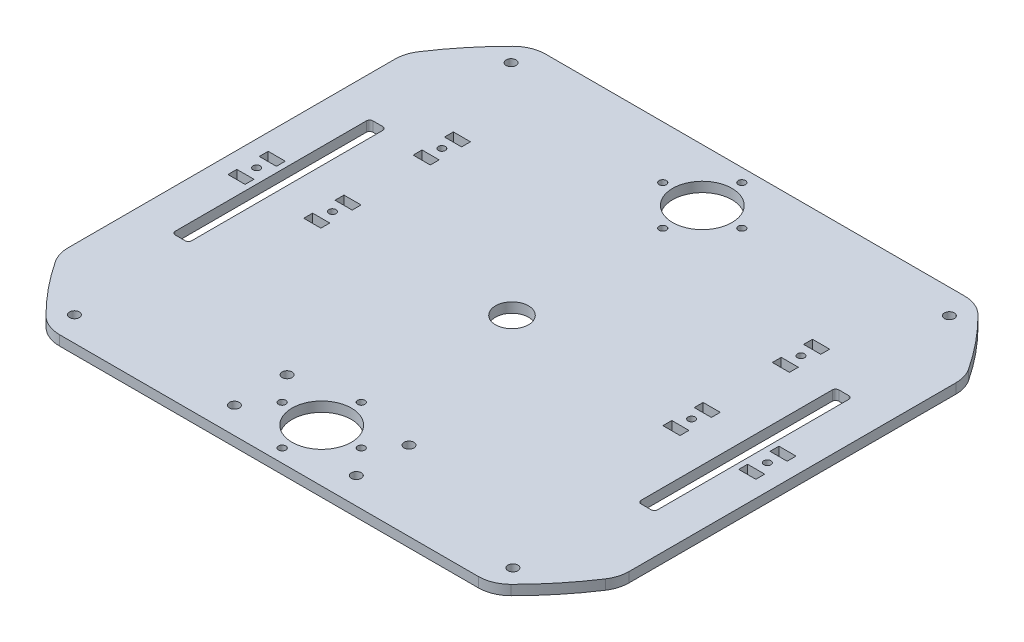
SolidWorks part; units mm, degrees
ref_plane "Front Plane" through (0, 0, 0) normal (0, 0, 1) x (1, 0, 0)
ref_plane "Top Plane" through (0, 0, 0) normal (0, 1, 0) x (1, 0, 0)
ref_plane "Right Plane" through (0, 0, 0) normal (1, 0, 0) x (0, 0, -1)
sketch "Sketch1" plane through (0, 0, 0) normal (0, 1, 0) x (1, 0, 0)
  circle A0 centre (0, 0) radius 100
  circle A1 centre (0, 0) radius 5
  dimension "D1" = 200
  dimension "D2" = 10
extrude "Boss-Extrude1" add sketch "Sketch1" along normal blind 3
sketch "Sketch2" plane through (0, 3, 0) normal (0, 1, 0) x (1, 0, 0)
  line L0 (75, 6) -> (80, 6) construction
  line L1 (75, 6) -> (75, 3.5) construction
  line L2 (75, 3.5) -> (80, 3.5) construction
  line L3 (80, 6) -> (80, 3.5) construction
  line L4 (75, -3.5) -> (80, -3.5) construction
  line L5 (75, -3.5) -> (75, -6) construction
  line L6 (75, -6) -> (80, -6) construction
  line L7 (80, -3.5) -> (80, -6) construction
  line L8 (66, -59.6098) -> (66, 6) construction
  line L9 (52, -3.5) -> (52, -6) construction
  line L10 (57, -6) -> (52, -6) construction
  line L11 (57, -3.5) -> (57, -6) construction
  line L12 (57, -3.5) -> (52, -3.5) construction
  line L13 (52, 6) -> (52, 3.5) construction
  line L14 (57, 3.5) -> (52, 3.5) construction
  line L15 (57, 6) -> (57, 3.5) construction
  line L16 (57, 6) -> (52, 6) construction
  line L17 (55.9387, 16.6) -> (52, 16.6) construction
  line L18 (57, 27.2) -> (52, 27.2) construction
  line L19 (57, 27.2) -> (57, 29.7) construction
  line L20 (57, 29.7) -> (52, 29.7) construction
  line L21 (52, 27.2) -> (52, 29.7) construction
  line L22 (57, 36.7) -> (52, 36.7) construction
  line L23 (57, 36.7) -> (57, 39.2) construction
  line L24 (57, 39.2) -> (52, 39.2) construction
  line L25 (52, 36.7) -> (52, 39.2) construction
  line L26 (0, 85.9128) -> (0, -59.0872) construction
  line L27 (-55.9387, 16.6) -> (-52, 16.6) construction
  line L28 (-66, -59.6098) -> (-66, 6) construction
  line L29 (-52, 36.7) -> (-52, 39.2) construction
  line L30 (-57, 39.2) -> (-52, 39.2) construction
  line L31 (-57, 36.7) -> (-57, 39.2) construction
  line L32 (-57, 36.7) -> (-52, 36.7) construction
  line L33 (-52, 27.2) -> (-52, 29.7) construction
  line L34 (-57, 29.7) -> (-52, 29.7) construction
  line L35 (-57, 27.2) -> (-57, 29.7) construction
  line L36 (-57, 27.2) -> (-52, 27.2) construction
  line L37 (-57, 6) -> (-52, 6) construction
  line L38 (-57, 6) -> (-57, 3.5) construction
  line L39 (-57, 3.5) -> (-52, 3.5) construction
  line L40 (-52, 6) -> (-52, 3.5) construction
  line L41 (-57, -3.5) -> (-52, -3.5) construction
  line L42 (-57, -3.5) -> (-57, -6) construction
  line L43 (-57, -6) -> (-52, -6) construction
  line L44 (-52, -3.5) -> (-52, -6) construction
  line L45 (-80, -3.5) -> (-80, -6) construction
  line L46 (-75, -6) -> (-80, -6) construction
  line L47 (-75, -3.5) -> (-75, -6) construction
  line L48 (-75, -3.5) -> (-80, -3.5) construction
  line L49 (-80, 6) -> (-80, 3.5) construction
  line L50 (-75, 3.5) -> (-80, 3.5) construction
  line L51 (-75, 6) -> (-75, 3.5) construction
  line L52 (-75, 6) -> (-80, 6) construction
  line L101 (-51.9, 36.6) -> (-51.9, 39.3)
  line L102 (-57.1, 39.3) -> (-51.9, 39.3)
  line L103 (-57.1, 36.6) -> (-57.1, 39.3)
  line L104 (-57.1, 36.6) -> (-51.9, 36.6)
  line L105 (-51.9, 27.1) -> (-51.9, 29.8)
  line L106 (-57.1, 29.8) -> (-51.9, 29.8)
  line L107 (-57.1, 27.1) -> (-57.1, 29.8)
  line L108 (-57.1, 27.1) -> (-51.9, 27.1)
  line L109 (-57.1, 6.1) -> (-51.9, 6.1)
  line L110 (-51.9, 6.1) -> (-51.9, 3.4)
  line L111 (-57.1, 3.4) -> (-51.9, 3.4)
  line L112 (-57.1, 6.1) -> (-57.1, 3.4)
  line L113 (-57.1, -3.4) -> (-51.9, -3.4)
  line L114 (-51.9, -3.4) -> (-51.9, -6.1)
  line L115 (-57.1, -6.1) -> (-51.9, -6.1)
  line L116 (-57.1, -3.4) -> (-57.1, -6.1)
  line L117 (-80.1, -3.4) -> (-80.1, -6.1)
  line L118 (-74.9, -6.1) -> (-80.1, -6.1)
  line L119 (-74.9, -3.4) -> (-74.9, -6.1)
  line L120 (-74.9, -3.4) -> (-80.1, -3.4)
  line L121 (-80.1, 6.1) -> (-80.1, 3.4)
  line L122 (-74.9, 3.4) -> (-80.1, 3.4)
  line L123 (-74.9, 6.1) -> (-74.9, 3.4)
  line L124 (-74.9, 6.1) -> (-80.1, 6.1)
  line L125 (57.1, 27.1) -> (51.9, 27.1)
  line L126 (51.9, 27.1) -> (51.9, 29.8)
  line L127 (57.1, 29.8) -> (51.9, 29.8)
  line L128 (57.1, 27.1) -> (57.1, 29.8)
  line L129 (57.1, 36.6) -> (51.9, 36.6)
  line L130 (51.9, 36.6) -> (51.9, 39.3)
  line L131 (57.1, 39.3) -> (51.9, 39.3)
  line L132 (57.1, 36.6) -> (57.1, 39.3)
  line L133 (74.9, 6.1) -> (80.1, 6.1)
  line L134 (80.1, 6.1) -> (80.1, 3.4)
  line L135 (74.9, 3.4) -> (80.1, 3.4)
  line L136 (74.9, 6.1) -> (74.9, 3.4)
  line L137 (74.9, -3.4) -> (80.1, -3.4)
  line L138 (80.1, -3.4) -> (80.1, -6.1)
  line L139 (74.9, -6.1) -> (80.1, -6.1)
  line L140 (74.9, -3.4) -> (74.9, -6.1)
  line L141 (51.9, -3.4) -> (51.9, -6.1)
  line L142 (57.1, -6.1) -> (51.9, -6.1)
  line L143 (57.1, -3.4) -> (57.1, -6.1)
  line L144 (57.1, -3.4) -> (51.9, -3.4)
  line L145 (51.9, 6.1) -> (51.9, 3.4)
  line L146 (57.1, 3.4) -> (51.9, 3.4)
  line L147 (57.1, 6.1) -> (57.1, 3.4)
  line L148 (57.1, 6.1) -> (51.9, 6.1)
  line L149 (-51.9, 3.4) -> (-51.9, -3.4) construction
  point P21 (54.5, 6)
  point P59 (-51.9, 0)
  dimension "D1" = 2.5
  dimension "D2" = 5
  dimension "D3" = 7
  dimension "D4" = 9
  dimension "D5" = 10.6
  dimension "D6" = 52
  dimension "D7" = 0.1
extrude "Cut-Extrude1" cut sketch "Sketch2" against normal through all
sketch "Sketch3" plane through (0, 3, 0) normal (0, 1, 0) x (1, 0, 0)
  line L0 (-85.1, 52.5166) -> (-85.1, -52.5166)
  line L1 (-80.1, 6.1) -> (-80.1, 3.4) construction
  line L2 (85.1, 52.5166) -> (85.1, -52.5166)
  line L3 (80.1, -6.1) -> (80.1, -3.4) construction
  line L4 (-67.5347, 73.75) -> (67.5347, 73.75)
  line L5 (-67.5347, -73.75) -> (67.5347, -73.75)
  line L7 (-67.5347, 73.75) -> (-67.5347, 115.6707)
  line L8 (-67.5347, 115.6707) -> (67.5347, 115.6707)
  line L9 (67.5347, 115.6707) -> (67.5347, 73.75)
  line L10 (85.1, 52.5166) -> (140.5183, 52.5166)
  line L11 (140.5183, 52.5166) -> (140.5183, -52.5166)
  line L12 (140.5183, -52.5166) -> (85.1, -52.5166)
  line L13 (67.5347, -73.75) -> (67.5347, -121.8499)
  line L14 (67.5347, -121.8499) -> (-67.5347, -121.8499)
  line L15 (-67.5347, -121.8499) -> (-67.5347, -73.75)
  line L16 (-85.1, -52.5166) -> (-115.9325, -52.5166)
  line L17 (-115.9325, -52.5166) -> (-115.9325, 52.5166)
  line L18 (-115.9325, 52.5166) -> (-85.1, 52.5166)
  circle A0 centre (0, 0) radius 100 construction
  point P7 (-80.1, 4.75)
  circle M53 centre (0, 0) radius 100
  dimension "D1" = 5
  dimension "D2" = 5
  dimension "D3" = 147.5
extrude "Cut-Extrude2" cut sketch "Sketch3" against normal through all contours L4 M53 | L0 M53 | L5 M53 | L2 M53
sketch "Sketch4" plane through (0, 3, 0) normal (0, 1, 0) x (1, 0, 0)
  line L0 (-74.9, 3.4) -> (-74.9, 6.1) construction
  line L1 (-73.2, 30) -> (-68.2, 30)
  line L2 (-73.2, 30) -> (-73.2, -30)
  line L3 (-73.2, -30) -> (-68.2, -30)
  line L4 (-68.2, 30) -> (-68.2, -30)
  line L5 (-74.9, 3.4) -> (-74.9, -3.4) construction
  line L6 (0, 0) -> (0, 73.75) construction
  line L7 (-67.5347, 73.75) -> (67.5347, 73.75) construction
  line L8 (73.2, 30) -> (68.2, 30)
  line L9 (73.2, 30) -> (73.2, -30)
  line L10 (73.2, -30) -> (68.2, -30)
  line L11 (68.2, 30) -> (68.2, -30)
  point P10 (-73.2, 0)
  point P11 (-74.9, 0)
  dimension "D1" = 1.7
  dimension "D2" = 5
  dimension "D3" = 60
extrude "Cut-Extrude3" cut sketch "Sketch4" against normal through all
fillet "Fillet3" radius 10 8 edges at (-85.1, 1.5, -52.5166) (-85.1, 1.5, 52.5166) (-67.5347, 1.5, 73.75) (67.5347, 1.5, 73.75) (85.1, 1.5, 52.5166) (85.1, 1.5, -52.5166) (67.5347, 1.5, -73.75) (-67.5347, 1.5, -73.75)
fillet "Fillet2" radius 1 8 edges at (68.2, 1.5, -30) (73.2, 1.5, -30) (68.2, 1.5, 30) (73.2, 1.5, 30) (-68.2, 1.5, 30) (-73.2, 1.5, 30) (-73.2, 1.5, -30) (-68.2, 1.5, -30)
sketch "Sketch5" plane through (0, 3, 0) normal (0, 1, 0) x (1, 0, 0)
  line L0 (-54.5, 36.6) -> (-54.5, 29.8) construction
  line L1 (-57.1, 36.6) -> (-51.9, 36.6) construction
  line L2 (-51.9, 29.8) -> (-57.1, 29.8) construction
  line L3 (-77.5, 3.4) -> (-77.5, -3.4) construction
  line L4 (-80.1, 3.4) -> (-74.9, 3.4) construction
  line L5 (-74.9, -3.4) -> (-80.1, -3.4) construction
  line L6 (-54.5, 3.4) -> (-54.5, -3.4) construction
  line L7 (-57.1, 3.4) -> (-51.9, 3.4) construction
  line L8 (-51.9, -3.4) -> (-57.1, -3.4) construction
  line L9 (0, 0) -> (0, 73.75) construction
  line L10 (-63.529, 73.75) -> (63.529, 73.75) construction
  line L11 (54.5, 3.4) -> (54.5, -3.4) construction
  line L12 (77.5, 3.4) -> (77.5, -3.4) construction
  line L13 (54.5, 36.6) -> (54.5, 29.8) construction
  circle A0 centre (-54.5, 33.2) radius 1.075
  circle A1 centre (-54.5, 0) radius 1.075
  circle A2 centre (-77.5, 0) radius 1.075
  circle A3 centre (77.5, 0) radius 1.075
  circle A4 centre (54.5, 0) radius 1.075
  circle A5 centre (54.5, 33.2) radius 1.075
  dimension "D1" = 2.15
extrude "Cut-Extrude4" cut sketch "Sketch5" against normal through all
sketch "Sketch6" plane through (0, 3, 0) normal (0, 1, 0) x (1, 0, 0)
  line L0 (-63.529, 73.75) -> (63.529, 73.75) construction
  line L1 (-85.1, 0) -> (85.1, 0) construction
  line L2 (-85.1, 49.5983) -> (-85.1, -49.5983) construction
  line L3 (85.1, 49.5983) -> (85.1, -49.5983) construction
  circle A0 centre (0, 57.75) radius 9
  circle A2 centre (0, 69.75) radius 1.1
  circle A3 centre (12, 57.75) radius 1.1
  circle A4 centre (0, 45.75) radius 1.1
  circle A5 centre (-12, 57.75) radius 1.1
  circle A6 centre (-12, -57.75) radius 1.1
  circle A7 centre (0, -45.75) radius 1.1
  circle A8 centre (12, -57.75) radius 1.1
  circle A9 centre (0, -69.75) radius 1.1
  circle A10 centre (0, -57.75) radius 9
  point P16 (0, 57.75)
  dimension "D1" = 18
  dimension "D2" = 16
  dimension "D4" = 12
  dimension "D3" = 2.2
  dimension "D5" = 4
extrude "Cut-Extrude5" cut sketch "Sketch6" against normal through all
sketch "IR Holder Holes Sketch" plane through (0, 3, 0) normal (0, 1, 0) x (1, 0, 0)
  line L0 (18.5, -73.75) -> (18.5, -65.75) construction
  line L1 (-16, -41.75) -> (16, -41.75)
  line L2 (-16, -41.75) -> (-16, -73.75)
  line L3 (-16, -73.75) -> (16, -73.75)
  line L4 (16, -41.75) -> (16, -73.75)
  line L5 (-16, -41.75) -> (16, -73.75) construction
  line L6 (-16, -73.75) -> (16, -41.75) construction
  line L7 (16, -73.75) -> (21, -73.75)
  line L8 (16, -73.75) -> (16, -41.75)
  line L9 (16, -41.75) -> (21, -41.75)
  line L10 (21, -73.75) -> (21, -41.75)
  line L11 (-16, -73.75) -> (-21, -73.75)
  line L12 (-16, -73.75) -> (-16, -41.75)
  line L13 (-16, -41.75) -> (-21, -41.75)
  line L14 (-21, -73.75) -> (-21, -41.75)
  line L15 (18.5, -41.75) -> (18.5, -49.75) construction
  line L16 (0, -73.75) -> (0, -41.75) construction
  circle A0 centre (18.5, -65.75) radius 1.5
  circle A1 centre (18.5, -49.75) radius 1.5
  circle A2 centre (-18.5, -65.75) radius 1.5
  circle A3 centre (-18.5, -49.75) radius 1.5
  point P0 (0, -57.75)
  dimension "D6" = 3
  dimension "D1" = 32
  dimension "D2" = 32
  dimension "D3" = 5
  dimension "D4" = 5
  dimension "D5" = 8
  dimension "D7" = 8
extrude "IR Holder Holes" cut sketch "IR Holder Holes Sketch" against normal up to next contours A3 | A2 | A0 | A1
sketch "Platform Holes Sketch" plane through (0, 3, 0) normal (0, 1, 0) x (1, 0, 0)
  line L0 (-63.529, 73.75) -> (-63.529, 66.25) construction
  line L1 (-63.529, 73.75) -> (63.529, 73.75)
  line L2 (-63.529, 73.75) -> (-63.529, -73.75) construction
  line L3 (-63.529, -73.75) -> (63.529, -73.75)
  line L4 (63.529, 73.75) -> (63.529, -73.75) construction
  line L5 (-63.529, 66.25) -> (-66.529, 66.25) construction
  line L6 (66.471, 66.25) -> (63.529, 66.25) construction
  line L7 (63.529, 73.75) -> (63.529, 66.25) construction
  line L8 (-66.529, -66.25) -> (-63.529, -66.25) construction
  line L9 (-63.529, -66.25) -> (-63.529, -73.75) construction
  line L10 (-63.529, -66.25) -> (-63.529, -73.75) construction
  line L11 (0, 73.75) -> (0, -73.75) construction
  circle A0 centre (-66.529, 66.25) radius 1.5
  circle A1 centre (66.471, 66.25) radius 1.5
  circle A4 centre (-66.3575, -67.2499) radius 1.5 [skipped]
  circle A5 centre (-66.529, -66.25) radius 1.5
  circle A6 centre (66.6425, -67.2499) radius 1.5 [skipped]
  circle A7 centre (66.529, -66.25) radius 1.5
  dimension "D3" = 3
  dimension "D6" = 133
  dimension "D7" = 3
  dimension "D1" = 7.5
  dimension "D2" = 3
  dimension "D8" = 3
  dimension "D9" = 7.5
  dimension "D4" = 2
  dimension "D5" = 2
extrude "Platform Holes" cut sketch "Platform Holes Sketch" against normal up to next contours A0 | A5 | A7 | A1
